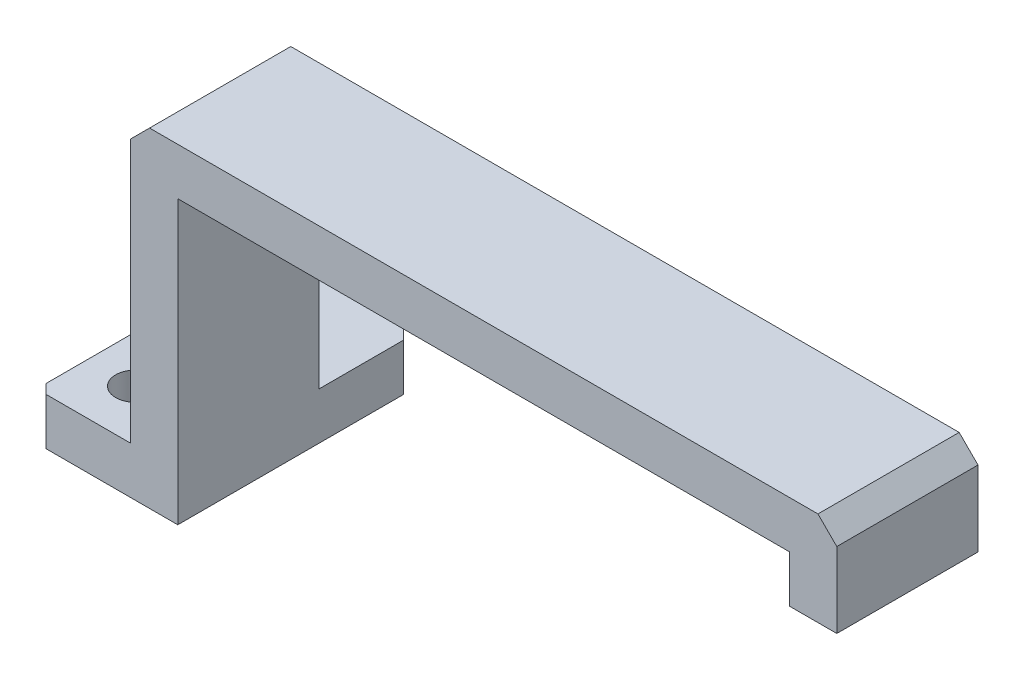
SolidWorks part; units mm, degrees
ref_plane "Front Plane" through (0, 0, 0) normal (0, 0, 1) x (1, 0, 0)
ref_plane "Top Plane" through (0, 0, 0) normal (0, 1, 0) x (1, 0, 0)
ref_plane "Right Plane" through (0, 0, 0) normal (1, 0, 0) x (0, 0, -1)
sketch "Sketch1" plane through (0, 0, 0) normal (0, 0, 1) x (1, 0, 0)
  line L0 (0, 17.5) -> (0, -17.5) construction
  line L1 (-37.5, -17.5) -> (37.5, -17.5)
  line L2 (-37.5, -12.5) -> (-37.5, 17.5)
  line L3 (-37.5, 17.5) -> (37.5, 17.5)
  line L4 (37.5, -12.5) -> (37.5, 17.5)
  line L5 (-37.5, -17.5) -> (37.5, 17.5) construction
  line L6 (-37.5, 17.5) -> (37.5, -17.5) construction
  line L7 (-37.5, -12.5) -> (-57.5, -12.5)
  line L8 (-32.5, -17.5) -> (32.5, -17.5)
  line L9 (-32.5, -17.5) -> (-32.5, 12.5)
  line L10 (-32.5, 12.5) -> (32.5, 12.5)
  line L11 (32.5, -17.5) -> (32.5, 12.5)
  line L12 (37.5, -17.5) -> (57.5, -17.5)
  line L14 (37.5, -12.5) -> (57.5, -12.5)
  line L15 (57.5, -17.5) -> (57.5, -12.5)
  line L16 (-57.5, -17.5) -> (-57.5, -12.5)
  line L17 (-37.5, -17.5) -> (-57.5, -17.5)
  point P0 (0, 0)
  dimension "D1" = 35
  dimension "D2" = 75
  dimension "D3" = 5
  dimension "D4" = 5
  dimension "D5" = 5
  dimension "D6" = 5
  dimension "D7" = 20
extrude "Boss-Extrude1" add sketch "Sketch1" along normal blind 30 contours L17 L1 L9 L10 L11 L12 L15 L14 L4 L3 L2 L7 L16
sketch "Sketch2" plane through (0, 17.5, 0) normal (0, 1, 0) x (1, 0, 0)
  line L0 (-37.5, -15) -> (37.5, -15) construction
  line L1 (-37.5, -30) -> (-37.5, 0) construction
  line L2 (37.5, -30) -> (37.5, 0) construction
  line L3 (0, 0) -> (0, -30) construction
  line L4 (-37.5, -30) -> (37.5, -30) construction
  line L6 (-25, -25) -> (25, -25)
  line L7 (-25, -25) -> (-25, -5)
  line L8 (-25, -5) -> (25, -5)
  line L9 (25, -25) -> (25, -5)
  line L10 (-25, -25) -> (25, -5) construction
  line L11 (-25, -5) -> (25, -25) construction
  point P11 (0, -15)
  dimension "D1" = 50
  dimension "D2" = 20
extrude "Cut-Extrude1" cut sketch "Sketch2" against normal blind 30
chamfer "Chamfer1" distance 2 angle 45 2 edges at (37.5, 17.5, 15) (-37.5, 17.5, 15)
sketch "Sketch3" plane through (0, -12.5, 0) normal (0, 1, 0) x (1, 0, 0)
  line L0 (-47.5, 0) -> (-47.5, -30) construction
  line L1 (-37.5, 0) -> (-57.5, 0) construction
  line L2 (-37.5, -30) -> (-57.5, -30) construction
  line L3 (47.5, 0) -> (47.5, -30) construction
  line L4 (37.5, 0) -> (57.5, 0) construction
  line L5 (37.5, -30) -> (57.5, -30) construction
  circle A0 centre (-47.5, -15) radius 2.1
  circle A1 centre (47.5, -15) radius 2.1
  dimension "D1" = 4.2
  dimension "D2" = 4.2
extrude "Cut-Extrude2" cut sketch "Sketch3" against normal blind 30
sketch "Sketch6" plane through (0, 17.5, 0) normal (0, 1, 0) x (1, 0, 0)
  line L0 (0, 0) -> (0, -30) construction
  line L1 (-35.5, -30) -> (35.5, -30) construction
  line L2 (-35.5, 0) -> (35.5, 0) construction
  line L3 (-2.5, -30) -> (2.5, -30)
  line L4 (-2.5, -30) -> (-2.5, 0)
  line L5 (-2.5, 0) -> (2.5, 0)
  line L6 (2.5, -30) -> (2.5, 0)
  line L7 (-2.5, -30) -> (2.5, 0) construction
  line L8 (-2.5, 0) -> (2.5, -30) construction
  point P5 (0, -15)
  dimension "D1" = 5
extrude "Boss-Extrude2" add sketch "Sketch6" against normal up to surface (5 mm away) up to face at (0, 12.5, 15)
sketch "Sketch7" plane through (0, 0, 30) normal (0, 0, 1) x (1, 0, 0)
  line L1 (-63.0947, -24.8231) -> (63.0947, -24.8231)
  line L2 (-63.0947, -24.8231) -> (-63.0947, 24.8231)
  line L3 (-63.0947, 24.8231) -> (63.0947, 24.8231)
  line L4 (63.0947, -24.8231) -> (63.0947, 24.8231)
  line L5 (-63.0947, -24.8231) -> (63.0947, 24.8231) construction
  line L6 (-63.0947, 24.8231) -> (63.0947, -24.8231) construction
  point P0 (0, 0)
extrude "Cut-Extrude3" cut sketch "Sketch7" against normal blind 15
sketch "Sketch8" plane through (0, -12.5, 0) normal (0, 1, 0) x (1, 0, 0)
  line L1 (-57.5, 0) -> (-37.5, 0)
  line L2 (-57.5, 0) -> (-57.5, -15)
  line L3 (-57.5, -15) -> (-37.5, -15)
  line L4 (-37.5, 0) -> (-37.5, -15)
extrude "Boss-Extrude3" add sketch "Sketch8" against normal through all
sketch "Sketch9" plane through (0, 17.5, 0) normal (0, 1, 0) x (1, 0, 0)
  line L1 (-35.5, 0) -> (35.5, 0)
  line L2 (-35.5, 0) -> (-35.5, -15)
  line L3 (-35.5, -15) -> (35.5, -15)
  line L4 (35.5, 0) -> (35.5, -15)
extrude "Boss-Extrude4" add sketch "Sketch9" against normal up to surface (5 mm away) up to face at (0, 12.5, 9.1667)
sketch "Sketch10" plane through (37.5, 0, 0) normal (1, 0, 0) x (0, 0, -1)
  line L0 (0, -12.5) -> (0, 15.5) construction
  line L1 (-15, 17.5) -> (0, 17.5)
  line L2 (-15, 17.5) -> (-15, 7.5)
  line L3 (-15, 7.5) -> (0, 7.5)
  line L4 (0, 17.5) -> (0, 7.5)
  line L6 (-15, 7.5) -> (0, 7.5)
  line L7 (-15, 7.5) -> (-15, -17.5)
  line L8 (-15, -17.5) -> (0, -17.5)
  line L9 (0, 7.5) -> (0, -17.5)
  line M3 (-15, 15.5) -> (-15, -12.5)
  line M4 (-15, -12.5) -> (0, -12.5)
  line M5 (0, -12.5) -> (0, 15.5)
  dimension "D1" = 10
extrude "Cut-Extrude4" cut sketch "Sketch10" against normal blind 27 and the other way blind 38 contours L3 M3 M4 M5 | L9 L7 L8 M4
sketch "Sketch11" plane through (0, -12.5, 0) normal (0, 1, 0) x (1, 0, 0)
  line L0 (-57.5, -7.5) -> (-37.5, -7.5) construction
  line L1 (-57.5, -15) -> (-57.5, 0) construction
  line L2 (-37.5, -15) -> (-37.5, 0) construction
  circle A0 centre (-47.5, -7.5) radius 2.1
  dimension "D1" = 4.2
extrude "Cut-Extrude5" cut sketch "Sketch11" against normal blind 27
sketch "Sketch12" plane through (0, -17.5, 0) normal (0, -1, 0) x (-1, 0, 0)
  line L0 (32.5, 0) -> (-32.5, 0) construction
  line L1 (57.5, -15) -> (0, -15)
  line L2 (57.5, -15) -> (57.5, 0)
  line L3 (57.5, 0) -> (0, 0)
  line L4 (0, -15) -> (0, 0)
  line L5 (57.5, -7.5) -> (0, -7.5) construction
  line L6 (47.5, -7.5) -> (47.5, -15) construction
  circle A0 centre (47.5, -7.5) radius 2.1
extrude "Boss-Extrude5" add sketch "Sketch12" against normal up to surface (5 mm away) contours A0 up to face at (-47.5, -12.5, 9.6)
sketch "Sketch13" plane through (0, -17.5, 0) normal (0, -1, 0) x (-1, 0, 0)
  line L0 (-32.5, -15) -> (32.5, -15) construction
  line L1 (0, -15) -> (57.5, -15)
  line L2 (0, -15) -> (0, 0)
  line L3 (0, 0) -> (57.5, 0)
  line L4 (57.5, -15) -> (57.5, 0)
  line L5 (57.5, -7.5) -> (0, -7.5) construction
  line L6 (57.5, -11) -> (0, -11) construction
  circle A0 centre (42.5, -11) radius 2.1
  circle A1 centre (42.5, -4) radius 2.1
  dimension "D2" = 4.2
  dimension "D1" = 4
  dimension "D3" = 15
extrude "Cut-Extrude6" cut sketch "Sketch13" against normal up to surface (5 mm away) contours A1 | A0 up to face at (-47.5, -12.5, 7.5)
sketch "Sketch14" plane through (0, -17.5, 0) normal (0, -1, 0) x (-1, 0, 0)
  line L0 (32.5, 0) -> (57.5, 0) construction
  line L4 (52.5, -15) -> (52.5, 0)
  line L6 (52.5, -15) -> (57.5, -15)
  line L7 (52.5, -15) -> (52.5, 0)
  line L8 (52.5, 0) -> (57.5, 0)
  line L9 (57.5, -15) -> (57.5, 0)
  circle A0 centre (42.5, -11) radius 2.1 construction
  line M3 (32.5, -15) -> (57.5, -15)
  line M4 (57.5, -15) -> (57.5, 0)
  line M5 (57.5, 0) -> (32.5, 0)
  dimension "D1" = 10
extrude "Cut-Extrude7" cut sketch "Sketch14" against normal blind 10 contours L4 M3 M4 M5
sketch "Sketch15" plane through (0, -12.5, 0) normal (0, 1, 0) x (1, 0, 0)
  line L0 (-52.5, -15) -> (-37.5, -15) construction
  line L4 (-47.5, 0) -> (-47.5, -15)
  line L6 (-47.5, 0) -> (-52.5, 0)
  line L7 (-47.5, 0) -> (-47.5, -15)
  line L8 (-47.5, -15) -> (-52.5, -15)
  line L9 (-52.5, 0) -> (-52.5, -15)
  circle A1 centre (-42.5, -4) radius 2.1 construction
  line M5 (-52.5, 0) -> (-52.5, -15)
  line M6 (-52.5, -15) -> (-37.5, -15)
  line M8 (-37.5, 0) -> (-52.5, 0)
  dimension "D1" = 5
extrude "Cut-Extrude8" cut sketch "Sketch15" against normal blind 10 contours L4 M8 M5 M6
sketch "Sketch16" plane through (0, -12.5, 0) normal (0, 1, 0) x (1, 0, 0)
  line L1 (-47.5, -15) -> (-37.5, -15)
  line L2 (-47.5, -15) -> (-47.5, 10)
  line L3 (-47.5, 10) -> (-37.5, 10)
  line L4 (-37.5, -15) -> (-37.5, 10)
  dimension "D1" = 25
extrude "Boss-Extrude6" add sketch "Sketch16" against normal through all
sketch "Sketch17" plane through (0, -12.5, 0) normal (0, 1, 0) x (1, 0, 0)
  line L0 (-47.5, 4.5) -> (-37.5, 4.5) construction
  line L1 (-47.5, 10) -> (-47.5, -15) construction
  line L2 (-37.5, 0) -> (-37.5, 10) construction
  line L3 (-47.5, -2.5) -> (-37.5, -2.5) construction
  line L4 (-37.5, -15) -> (-37.5, 0) construction
  line L5 (-42.5, 10) -> (-42.5, -15) construction
  line L6 (-37.5, 10) -> (-47.5, 10) construction
  line L7 (-47.5, -15) -> (-37.5, -15) construction
  line L8 (-47.5, -9.5) -> (-37.5, -9.5) construction
  line L9 (-37.5, -15) -> (-37.5, 0) construction
  circle A0 centre (-42.5, 4.5) radius 2.1
  circle A1 centre (-42.5, -9.5) radius 2.1
  dimension "D3" = 4.2
  dimension "D4" = 4.2
  dimension "D1" = 7
  dimension "D2" = 7
extrude "Cut-Extrude9" cut sketch "Sketch17" against normal blind 30
sketch "Sketch18" plane through (-37.5, 0, 0) normal (1, 0, 0) x (0, 0, -1)
  line L1 (0, -12.5) -> (10, -12.5)
  line L2 (0, -12.5) -> (0, -17.5)
  line L3 (0, -17.5) -> (10, -17.5)
  line L4 (10, -12.5) -> (10, -17.5)
extrude "Boss-Extrude7" add sketch "Sketch18" along normal up to surface (5 mm away) up to face at (-32.5, -2.5, 7.5)
chamfer "Chamfer3" distance 1 angle 45 2 edges at (-47.5, -15, -10) (-47.5, -15, 15)
chamfer "Chamfer4" distance 1 angle 45 1 edges at (-32.5, -15, -10)
